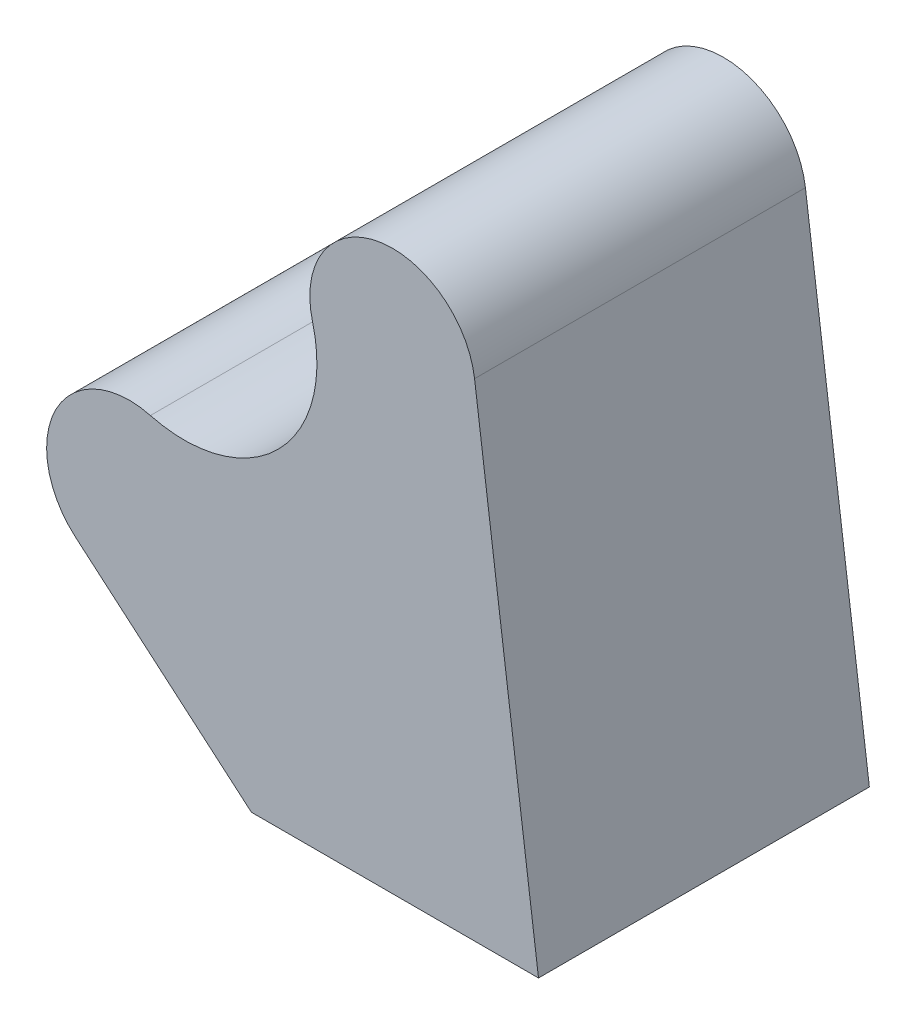
SolidWorks part; units mm, degrees
ref_plane "前视基准面" through (0, 0, 0) normal (0, 0, 1) x (1, 0, 0)
ref_plane "上视基准面" through (0, 0, 0) normal (0, 1, 0) x (1, 0, 0)
ref_plane "右视基准面" through (0, 0, 0) normal (1, 0, 0) x (0, 0, -1)
sketch "草图1" plane through (0, 0, 0) normal (0, 0, 1) x (1, 0, 0)
  line L0 (14.7542, -25.7619) -> (49.4647, -25.7619)
  line L1 (49.4647, -25.7619) -> (41.7347, 33.1214)
  line L2 (-6.4965, -7.6023) -> (14.7542, -25.7619)
  line L3 (0, 0) -> (31.8198, 31.8198) construction
  arc A0 (22.1492, 29.2743) -> (41.7347, 33.1214) centre (31.8198, 31.8198) cw
  arc A1 (2.5455, 9.6706) -> (22.1492, 29.2743) centre (6.6305, 25.1894) ccw
  arc A2 (2.5455, 9.6706) -> (-6.4965, -7.6023) centre (0, 0) ccw
  dimension "D2" = 10
  dimension "D1" = 45
  dimension "D3" = 45
extrude "凸台-拉伸1" add sketch "草图1" along normal blind 40
